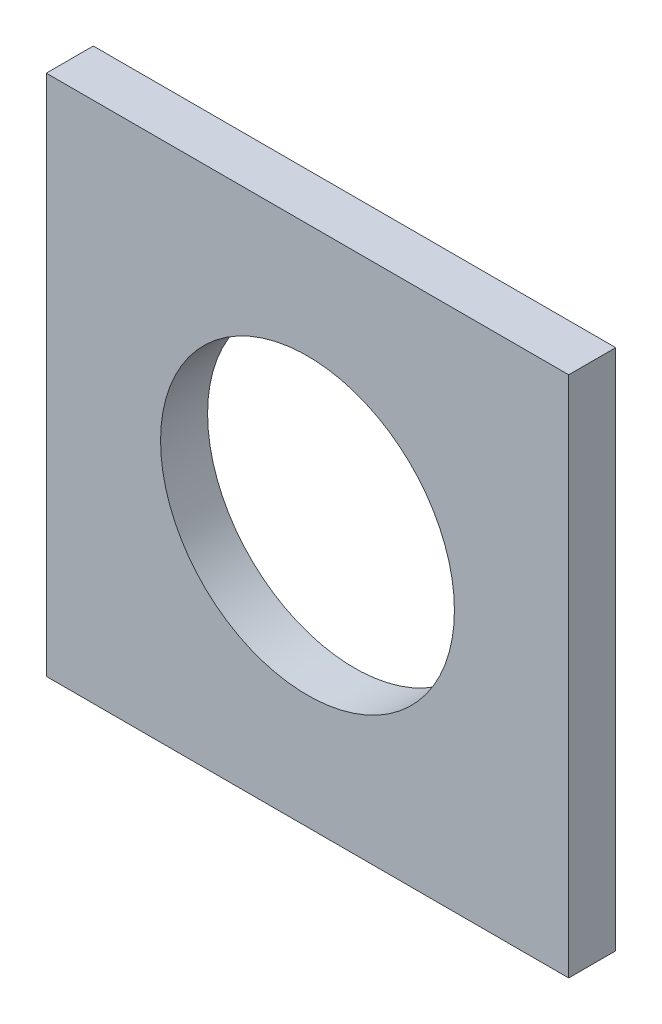
SolidWorks part; units mm, degrees
ref_plane "Front Plane" through (0, 0, 0) normal (0, 0, 1) x (1, 0, 0)
ref_plane "Top Plane" through (0, 0, 0) normal (0, 1, 0) x (1, 0, 0)
ref_plane "Right Plane" through (0, 0, 0) normal (1, 0, 0) x (0, 0, -1)
sketch "Sketch1" plane through (0, 0, 0) normal (0, 0, 1) x (1, 0, 0)
  line L1 (-18.8976, 19.0331) -> (31.9024, 19.0331)
  line L2 (-18.8976, 19.0331) -> (-18.8976, -31.7669)
  line L3 (-18.8976, -31.7669) -> (31.9024, -31.7669)
  line L4 (31.9024, 19.0331) -> (31.9024, -31.7669)
  dimension "D1" = 50.8
  dimension "D2" = 50.8
extrude "Boss-Extrude1" add sketch "Sketch1" along normal blind 4.572
sketch "Sketch2" plane through (0, 0, 0) normal (0, 0, -1) x (-1, 0, 0)
  line L0 (-6.5024, 19.0331) -> (-6.5024, -31.7669)
  line L1 (-31.9024, 19.0331) -> (18.8976, 19.0331) construction
  line L2 (18.8976, -31.7669) -> (-31.9024, -31.7669) construction
  line L3 (-31.9024, -6.3669) -> (18.8976, -6.3669)
  line L4 (-31.9024, -31.7669) -> (-31.9024, 19.0331) construction
  line L5 (18.8976, 19.0331) -> (18.8976, -31.7669) construction
  circle A0 centre (-6.5024, -6.3669) radius 14.2875
  dimension "D1" = 28.575
extrude "Cut-Extrude1" cut sketch "Sketch2" against normal blind 4.572 contours L0 A0 L3 | L3 A0 L0 | L0 A0 L3 | L3 A0 L0
